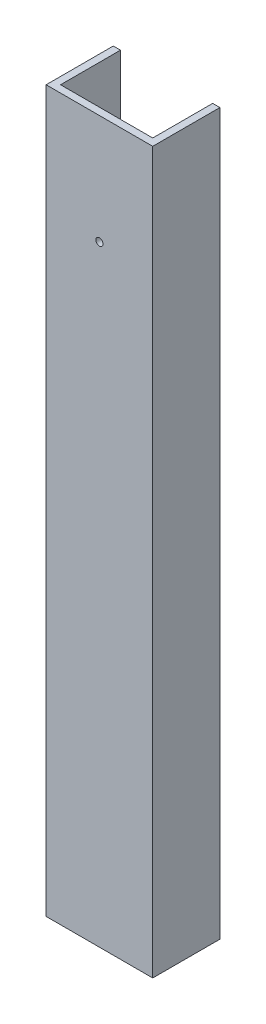
SolidWorks part; units mm, degrees
ref_plane "Alzado" through (0, 0, 0) normal (0, 0, 1) x (1, 0, 0)
ref_plane "Planta" through (0, 0, 0) normal (0, 1, 0) x (1, 0, 0)
ref_plane "Vista lateral" through (0, 0, 0) normal (1, 0, 0) x (0, 0, -1)
sketch "Croquis1" plane through (0, 0, 0) normal (0, 1, 0) x (1, 0, 0)
  line L1 (-18.5, -11.65) -> (18.5, -11.65)
  line L2 (-18.5, -11.65) -> (-18.5, 11.65)
  line L3 (-18.5, 11.65) -> (18.5, 11.65)
  line L4 (18.5, -11.65) -> (18.5, 11.65)
  line L5 (-18.5, -11.65) -> (18.5, 11.65) construction
  line L6 (-18.5, 11.65) -> (18.5, -11.65) construction
  point P0 (0, 0)
  dimension "D1" = 23.3
  dimension "D2" = 37
extrude "Saliente-Extruir1" add sketch "Croquis1" along normal blind 250
sketch "Croquis2" plane through (0, 250, 0) normal (0, 1, 0) x (1, 0, 0)
  line L0 (18.5, 11.65) -> (-18.5, 11.65) construction
  line L1 (-16, 11.65) -> (16, 11.65)
  line L2 (-16, 11.65) -> (-16, -9.15)
  line L3 (-16, -9.15) -> (16, -9.15)
  line L4 (16, 11.65) -> (16, -9.15)
  line L5 (-18.5, 11.65) -> (-18.5, -11.65) construction
  line L6 (18.5, -11.65) -> (18.5, 11.65) construction
  line L7 (-18.5, -11.65) -> (18.5, -11.65) construction
  dimension "D1" = 2.5
  dimension "D2" = 2.5
  dimension "D3" = 2.5
extrude "Cortar-Extruir1" cut sketch "Croquis2" against normal blind 250
sketch "Croquis3" plane through (0, 0, 11.65) normal (0, 0, 1) x (1, 0, 0)
  line L0 (0, 0) -> (0, 220) construction
  line L1 (0, -12.815) -> (0, 12.815) construction
  line L2 (-18.5, 250) -> (18.5, 250) construction
  circle A0 centre (0, 212) radius 1.25
  dimension "D2" = 2.5
  dimension "D3" = 38
  dimension "D1" = 220
extrude "Cortar-Extruir2" cut sketch "Croquis3" against normal blind 250 contours A0
sketch "Croquis4" plane through (0, 0, 11.65) normal (0, 0, 1) x (1, 0, 0)
  line L0 (-18.5, 230.2175) -> (-18.5, 212.9642)
  line L1 (-18.5, 250) -> (-18.5, 0) construction
  line L2 (-18.5, 212.9642) -> (18.5, 212.9642)
  line L3 (18.5, 250) -> (18.5, 0) construction
  line L4 (18.5, 212.9642) -> (18.5, 230.2175)
  line L6 (-18.5, 230.2175) -> (18.5, 212.9642)
  point P9 (22.3357, 199.2061)
  point P10 (19.0492, 198.568)
  dimension "D1" = 25
